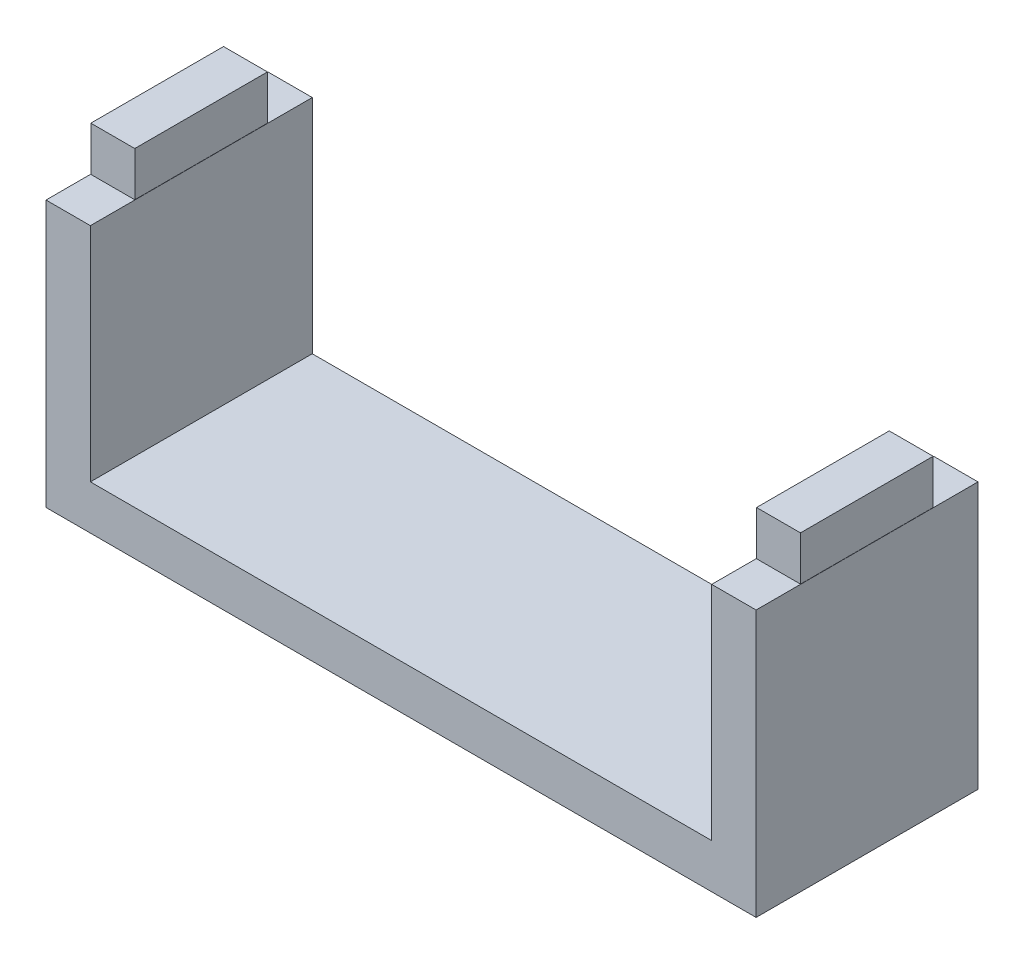
SolidWorks part; units mm, degrees
ref_plane "Front Plane" through (0, 0, 0) normal (0, 0, 1) x (1, 0, 0)
ref_plane "Top Plane" through (0, 0, 0) normal (0, 1, 0) x (1, 0, 0)
ref_plane "Right Plane" through (0, 0, 0) normal (1, 0, 0) x (0, 0, -1)
sketch "Sketch1" plane through (0, 0, 0) normal (0, 1, 0) x (1, 0, 0)
  line L1 (80, -25) -> (-80, -25)
  line L2 (80, -25) -> (80, 25)
  line L3 (80, 25) -> (-80, 25)
  line L4 (-80, -25) -> (-80, 25)
  line L5 (80, -25) -> (-80, 25) construction
  line L6 (80, 25) -> (-80, -25) construction
  point P0 (0, 0)
  dimension "D1" = 160
  dimension "D2" = 50
extrude "Boss-Extrude1" add sketch "Sketch1" along normal blind 10
sketch "Sketch2" plane through (0, 10, 0) normal (0, 1, 0) x (1, 0, 0)
  line L0 (0, 25) -> (0, -25) construction
  line L1 (80, 25) -> (-80, 25) construction
  line L2 (-80, -25) -> (80, -25) construction
  line L3 (-80, 25) -> (-80, -25) construction
  line L4 (-80, 25) -> (-70, 25)
  line L5 (-80, 25) -> (-80, -25)
  line L6 (-80, -25) -> (-70, -25)
  line L7 (-70, 25) -> (-70, -25)
  line L8 (80, -25) -> (70, -25)
  line L9 (70, 25) -> (70, -25)
  line L10 (80, 25) -> (70, 25)
  line L11 (80, 25) -> (80, -25)
  dimension "D1" = 50
  dimension "D2" = 10
extrude "Boss-Extrude2" add sketch "Sketch2" along normal blind 50
sketch "Sketch3" plane through (0, 60, 0) normal (0, 1, 0) x (1, 0, 0)
  line L0 (0, -25) -> (0, 25) construction
  line L1 (-70, -25) -> (70, -25) construction
  line L2 (70, 25) -> (-70, 25) construction
  line L4 (-70.05, -14.95) -> (-79.95, -14.95)
  line L5 (-70.05, -14.95) -> (-70.05, 14.95)
  line L6 (-70.05, 14.95) -> (-79.95, 14.95)
  line L7 (-79.95, -14.95) -> (-79.95, 14.95)
  line L10 (70.05, 14.95) -> (79.95, 14.95)
  line L11 (79.95, -14.95) -> (79.95, 14.95)
  line L12 (70.05, -14.95) -> (79.95, -14.95)
  line L13 (70.05, -14.95) -> (70.05, 14.95)
  line L14 (-70.05, 0) -> (-79.95, 0) construction
  line L16 (-70, 25) -> (-80, 25) construction
  line L21 (-75, -14.95) -> (-75, 14.95) construction
  line L25 (-70, -25) -> (-70, 25) construction
  dimension "D1" = 29.9
  dimension "D2" = 25
  dimension "D3" = 9.9
  dimension "D4" = 5
extrude "Boss-Extrude3" add sketch "Sketch3" along normal blind 10
